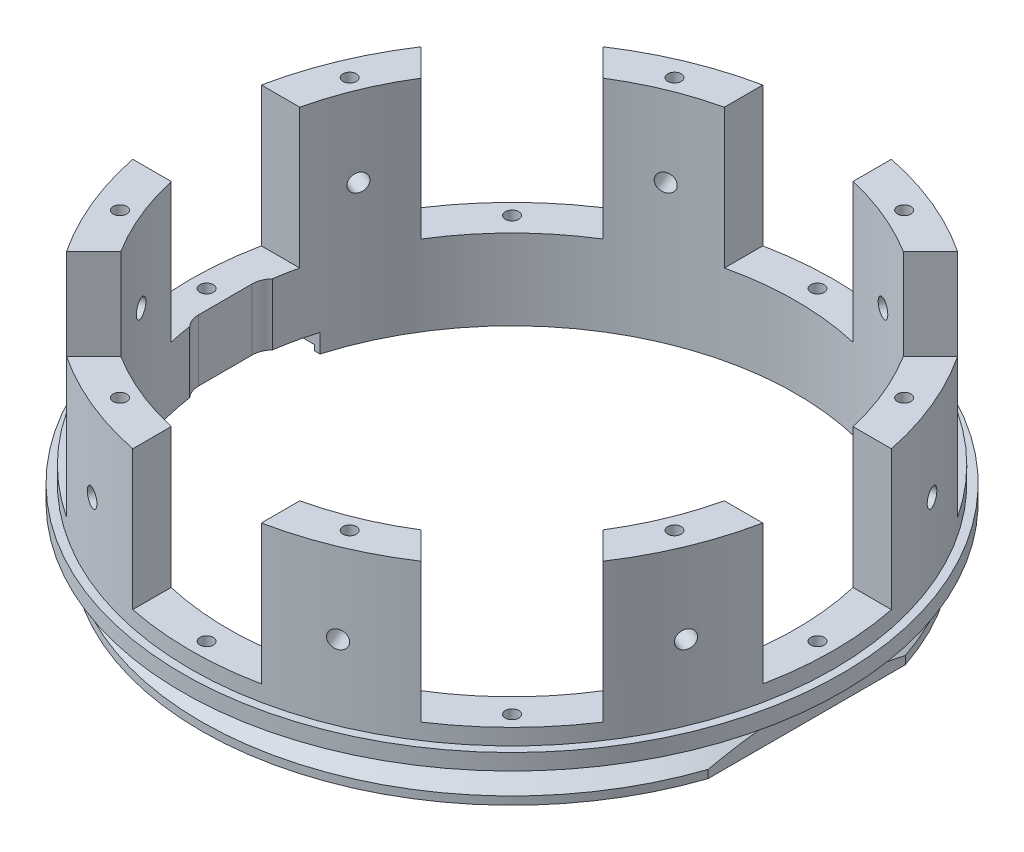
SolidWorks part; units mm, degrees
ref_plane "Ebene vorne" through (0, 0, 0) normal (0, 0, 1) x (1, 0, 0)
ref_plane "Ebene oben" through (0, 0, 0) normal (0, 1, 0) x (1, 0, 0)
ref_plane "Ebene rechts" through (0, 0, 0) normal (1, 0, 0) x (0, 0, -1)
sketch "Skizze1" plane through (0, 0, 0) normal (0, 0, 1) x (1, 0, 0)
  line L0 (-53, -1) -> (-53, 40)
  line L3 (-53, 40) -> (-60, 40)
  line L4 (-61.5, 11) -> (-61.5, 8)
  line L5 (-61.5, 8) -> (-55, 8)
  line L6 (-55, 8) -> (-55, 3.6006)
  line L7 (-55, 3.6006) -> (-58, 1.5)
  line L8 (-58, 1.5) -> (-58, 0)
  line L9 (-58, 0) -> (-54, 0)
  line L10 (-54, 0) -> (-54, -1)
  line L11 (-54, -1) -> (-53, -1)
  line L12 (-60, 40) -> (-60, 11)
  line L13 (-60, 11) -> (-61.5, 11)
  line L14 (0, 0) -> (0, 11.1018) construction
  dimension "D1" = 61.5
  dimension "D2" = 60
  dimension "D3" = 54
  dimension "D4" = 35
  dimension "D5" = 8
  dimension "D6" = 1.5
  dimension "D7" = 40
  dimension "D8" = 3
  dimension "D9" = 3
  dimension "D11" = 53
  dimension "D12" = 55
  dimension "D14" = 1
revolve "Rotation1" add sketch "Skizze1" angle 360 about L14
sketch "Skizze2" plane through (0, 0, 0) normal (1, 0, 0) x (0, 0, -1)
  line L0 (60, 40) -> (-60, 40) construction
  line L1 (12, 40) -> (-12, 40)
  line L2 (12, 40) -> (12, 14)
  line L3 (12, 14) -> (-12, 14)
  line L4 (-12, 40) -> (-12, 14)
  line L5 (0, 0) -> (0, 14) construction
  dimension "D1" = 26
  dimension "D2" = 24
extrude "Schnitt-Linear austragen1" cut sketch "Skizze2" against normal through all
pattern_circular "Kreismuster1" count 8 every 45 about axis through (0, 0, 0) along (0, 1, 0) of "Schnitt-Linear austragen1"
ref_plane "Ebene1" through (20.0091, 0, 48.3062) normal (-0.3827, 0, -0.9239) x (-0.9239, 0, 0.3827)
sketch "Skizze3" plane through (20.0091, 0, 48.3062) normal (-0.3827, 0, -0.9239) x (-0.9239, 0, 0.3827)
  line L0 (0, 25) -> (0, 0) construction
  line L1 (60, 11) -> (-60, 11) construction
  circle A0 centre (0, 25) radius 1.65
  dimension "D1" = 3.3
  dimension "D2" = 14
extrude "Schnitt-Linear austragen2" cut sketch "Skizze3" against normal through all
pattern_circular "Kreismuster2" count 8 over 360 about axis through (0, 0, 0) along (0, -1, 0) of "Schnitt-Linear austragen2"
sketch "Skizze4" plane through (0, 14, 0) normal (0, -1, 0) x (-1, 0, 0)
  line L0 (0, 60) -> (-7.1254, 60) construction
  line L1 (0, 57) -> (0, 60) construction
  line L2 (-57, 0) -> (57, 0) construction
  circle A0 centre (0, 57) radius 1.25
  circle A1 centre (40.3051, 40.3051) radius 1.25
  circle A2 centre (0, 0) radius 60 construction
  circle A3 centre (57, 0) radius 1.25
  circle A4 centre (40.3051, -40.3051) radius 1.25
  circle A5 centre (0, -57) radius 1.25
  circle A6 centre (-40.3051, -40.3051) radius 1.25
  circle A7 centre (-57, 0) radius 1.25
  circle A8 centre (-40.3051, 40.3051) radius 1.25
  dimension "D1" = 2.5
  dimension "D2" = 3
  dimension "D3" = 8
extrude "Schnitt-Linear austragen3" cut sketch "Skizze4" along normal up to surface (6 mm away) and the other way through all up to face at (0, 8, -55)
sketch "Skizze5" plane through (0, 0, 0) normal (0, -1, 0) x (1, 0, 0)
  line L0 (55, 18.412) -> (55, -18.412)
  line L1 (55, 18.412) -> (58, 18.412)
  line L2 (55, -18.412) -> (58, -18.412)
  line L3 (58, 18.412) -> (58, -18.412)
  circle A0 centre (0, 0) radius 58 construction
  point P6 (58, 0)
  dimension "D1" = 3
extrude "Schnitt-Linear austragen4" cut sketch "Skizze5" against normal up to next
sketch "Skizze6" plane through (0, 0, 0) normal (0, -1, 0) x (1, 0, 0)
  line L0 (-50.8331, -15) -> (-50.8331, 15)
  line L1 (-50.8331, -15) -> (-58, -15)
  line L2 (-50.8331, 15) -> (-58, 15)
  line L3 (-58, -15) -> (-58, 15)
  arc A1 (55, 18.412) -> (55, -18.412) centre (0, 0) ccw construction
  circle A3 centre (0, 0) radius 53 construction
  dimension "D1" = 30
extrude "Schnitt-Linear austragen5" cut sketch "Skizze6" against normal blind 2.5 and the other way through all
sketch "Skizze12" plane through (0, 40, 0) normal (0, 1, 0) x (1, 0, 0)
  line L0 (-51.7373, -21.4303) -> (0, 0) construction
  line L2 (51.7373, -21.4303) -> (-51.7373, 21.4303) construction
  circle A0 centre (-51.7373, -21.4303) radius 1.25
  arc A1 (-51.6236, -12) -> (-44.9887, -28.0181) centre (0, 0) ccw construction
  arc A2 (-51.6236, -12) -> (-44.9887, -28.0181) centre (0, 0) ccw construction
  circle A3 centre (-51.7373, 21.4303) radius 1.25
  circle A4 centre (-21.4303, 51.7373) radius 1.25
  circle A5 centre (21.4303, 51.7373) radius 1.25
  circle A6 centre (51.7373, 21.4303) radius 1.25
  circle A7 centre (51.7373, -21.4303) radius 1.25
  circle A8 centre (21.4303, -51.7373) radius 1.25
  circle A9 centre (-21.4303, -51.7373) radius 1.25
  point P9 (-48.9656, -20.2822)
  dimension "D1" = 2.5
  dimension "D2" = 56
  dimension "D3" = 8
extrude "Schnitt-Linear austragen6" cut sketch "Skizze12" against normal blind 10
sketch "Skizze13" plane through (0, 2.5, 0) normal (0, -1, 0) x (1, 0, 0)
  line L0 (-53.5, -5) -> (-53.5, 5)
  line L2 (-45.5, 5) -> (-45.5, -5)
  arc A2 (-53.5, -5) -> (-45.5, -5) centre (-49.5, -5) ccw
  arc A6 (-45.5, 5) -> (-53.5, 5) centre (-49.5, 5) ccw
  circle A7 centre (-49.5, 5) radius 4 construction
  dimension "D3" = 0
  dimension "D1" = 8
  dimension "D2" = 0
extrude "Schnitt-Linear austragen7" cut sketch "Skizze13" against normal up to next
